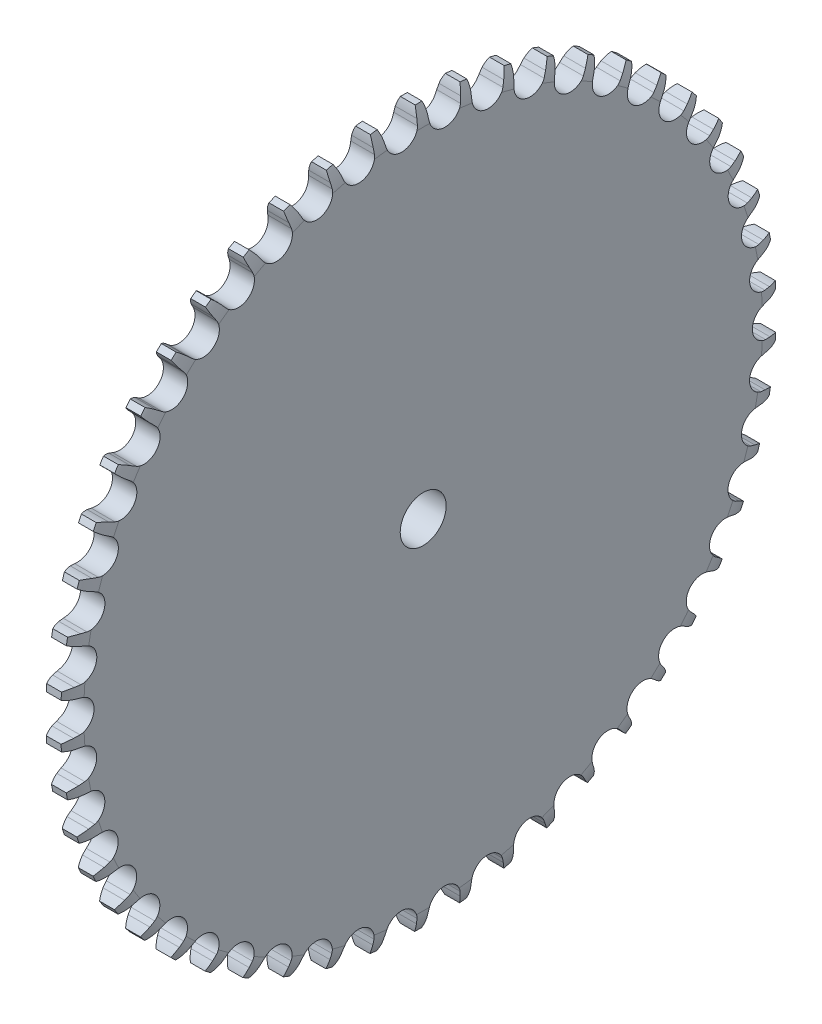
SolidWorks part; units mm, degrees
ref_plane "Front Plane" through (0, 0, 0) normal (0, 0, 1) x (1, 0, 0)
ref_plane "Top Plane" through (0, 0, 0) normal (0, 1, 0) x (1, 0, 0)
ref_plane "Right Plane" through (0, 0, 0) normal (1, 0, 0) x (0, 0, -1)
sketch "Sketch1" plane through (0, 0, 0) normal (0, 0, 1) x (1, 0, 0)
  line L0 (0, 0) -> (0, 73.8414)
  line L1 (-1.0423, 77.85) -> (-4.2577, 77.85)
  line L2 (-5.3, 73.8414) -> (-5.3, 20)
  line L3 (-5.3, 20) -> (-35.3, 20)
  line L4 (-35.3, 20) -> (-35.3, 0)
  line L5 (-35.3, 0) -> (0, 0)
  line L6 (0, 0) -> (22.8181, 0) construction
  arc A0 (-5.3, 73.8414) -> (-4.2577, 77.85) centre (4.6895, 73.3839) cw
  arc A1 (0, 73.8414) -> (-1.0423, 77.85) centre (-9.9895, 73.3839) ccw
  dimension "D5" = 10
  dimension "D1" = 35.3
  dimension "D2" = 30
  dimension "D3" = 20
  dimension "D4" = 155.7
revolve "Revolve1" add sketch "Sketch1" angle 360 about L6
sketch "Sketch2" plane through (-35.3, 0, 0) normal (-1, 0, 0) x (0, 0, 1)
  circle A0 centre (0, 0) radius 5
  dimension "D1" = 10
extrude "Cut-Extrude1" cut sketch "Sketch2" against normal blind 93
sketch "Sketch4" plane through (-35.3, 0, 0) normal (-1, 0, 0) x (0, 0, 1)
  line L0 (0, 0) -> (0, 75.845) construction
  line L1 (0, 0) -> (-4.7625, 74.9583) construction
  line L2 (0, 0) -> (4.7625, 74.9583) construction
  line L3 (-1.1687, 75.836) -> (-1.2768, 74.6426)
  line L4 (1.1687, 75.836) -> (1.2884, 75.3836)
  line L5 (-8.4385, 75.3741) -> (-8.1803, 74.204)
  arc A0 (-8.4385, 75.3741) -> (-1.1687, 75.836) centre (0, 0) ccw
  arc A1 (-8.1803, 74.204) -> (-1.2768, 74.6426) centre (-4.7625, 74.9583) ccw
  circle A2 centre (4.7625, 74.9583) radius 3.5
  arc A3 (-1.1687, 75.836) -> (-0.796, 77.8459) centre (9.7865, 74.844) cw
  circle A4 centre (0, 0) radius 77.85 construction
  arc A5 (1.1687, 75.836) -> (0.796, 77.8459) centre (-9.7865, 74.844) ccw
  arc A6 (-8.4385, 75.3741) -> (-9.0626, 77.3207) centre (-19.18, 73.0036) ccw
  arc A7 (-9.0626, 77.3207) -> (-0.796, 77.8459) centre (0, 0) cw
  dimension "D1" = 151.69
  dimension "D3" = 7
  dimension "D4" = 7
  dimension "D6" = 11
  dimension "D2" = 9.525
  dimension "D5" = 20
extrude "Cut-Extrude2" cut sketch "Sketch4" against normal blind 50 contours A7 A3 L3 A1 L5 A6
pattern_circular "CirPattern2" count 50 over 360 about axis through (0, 0, 0) along (1, 0, 0) of "Cut-Extrude2"
sketch "Sketch5" plane through (-35.3, 0, 0) normal (-1, 0, 0) x (0, 0, 1)
  line L1 (0, 7) -> (-2.85, 7)
  line L2 (-2.85, 7) -> (-2.85, 9.5)
  line L3 (-2.85, 9.5) -> (2.85, 9.5)
  line L4 (2.85, 9.5) -> (2.85, 7)
  line L5 (2.85, 7) -> (0, 7)
  line L7 (6.0622, -3.5) -> (7.4872, -1.0318)
  line L8 (7.4872, -1.0318) -> (9.6522, -2.2818)
  line L9 (9.6522, -2.2818) -> (6.8022, -7.2182)
  line L10 (6.8022, -7.2182) -> (4.6372, -5.9682)
  line L11 (4.6372, -5.9682) -> (6.0622, -3.5)
  line L13 (-6.0622, -3.5) -> (-7.4872, -1.0318)
  line L14 (-7.4872, -1.0318) -> (-9.6522, -2.2818)
  line L15 (-9.6522, -2.2818) -> (-6.8022, -7.2182)
  line L16 (-6.8022, -7.2182) -> (-4.6372, -5.9682)
  line L17 (-4.6372, -5.9682) -> (-6.0622, -3.5)
  dimension "D6" = 5.7
  dimension "D7" = 2.5
  dimension "D8" = 2.85
  dimension "D9" = 2.85
  dimension "D10" = 2.5
  dimension "D11" = 5.7
  dimension "D12" = 2.5
  dimension "D13" = 5.7
  dimension "D14" = 2.85
extrude "Cut-Extrude3" cut sketch "Sketch5" against normal blind 12.85
ref_plane "Plane1" through (0, 20, 0) normal (0, 1, 0) x (1, 0, 0)
sketch "Sketch6" plane through (0, 20, 0) normal (0, 1, 0) x (1, 0, 0)
  circle A0 centre (-20.3, 0) radius 3
  dimension "D1" = 6
extrude "Cut-Extrude4" cut sketch "Sketch6" against normal blind 4.5
sketch "Sketch7" plane through (0, 20, 0) normal (0, 1, 0) x (1, 0, 0)
  circle A0 centre (-20.3, 0) radius 1.95
  dimension "D1" = 3.9
extrude "Cut-Extrude5" cut sketch "Sketch7" against normal up to next
sketch "Sketch8" plane through (-35.3, 0, 0) normal (-1, 0, 0) x (0, 0, 1)
  line L0 (-2.85, 9.5) -> (2.85, 9.5)
  line L1 (2.85, 9.5) -> (2.85, 7)
  line L2 (2.85, 7) -> (-2.85, 7)
  line L3 (-2.85, 7) -> (-2.85, 9.5)
  line L4 (7.4872, -1.0318) -> (4.6372, -5.9682)
  line L5 (4.6372, -5.9682) -> (6.8022, -7.2182)
  line L6 (4.6372, -5.9682) -> (6.8022, -7.2182) construction
  line L7 (4.6372, -5.9682) -> (6.8022, -7.2182) construction
  line L8 (6.8022, -7.2182) -> (9.6522, -2.2818)
  line L9 (9.6522, -2.2818) -> (7.4872, -1.0318)
  line L10 (-7.4872, -1.0318) -> (-9.6522, -2.2818)
  line L11 (-9.6522, -2.2818) -> (-6.8022, -7.2182)
  line L12 (-6.8022, -7.2182) -> (-4.6372, -5.9682)
  line L13 (-4.6372, -5.9682) -> (-7.4872, -1.0318)
extrude "Cut-Extrude6" cut sketch "Sketch8" against normal blind 17.85
ref_plane "Plane2" through (0, -10, 17.3205) normal (0, -0.5, 0.866) x (-1, 0, 0)
sketch "Sketch9" plane through (0, -10, 17.3205) normal (0, -0.5, 0.866) x (-1, 0, 0)
  circle A0 centre (20.3, 0) radius 3
  dimension "D1" = 6
extrude "Cut-Extrude7" cut sketch "Sketch9" against normal blind 4.5
sketch "Sketch10" plane through (0, -10, 17.3205) normal (0, -0.5, 0.866) x (-1, 0, 0)
  circle A0 centre (20.3, 0) radius 1.95
  dimension "D1" = 3.9
extrude "Cut-Extrude8" cut sketch "Sketch10" against normal up to next
sketch "Sketch11" plane through (0, -10, 17.3205) normal (0, -0.5, 0.866) x (-1, 0, 0)
  circle A0 centre (20.3, 0) radius 1.95
  dimension "D1" = 3.9
extrude "Cut-Extrude9" cut sketch "Sketch11" against normal up to next
ref_plane "Plane3" through (0, -10, -17.3205) normal (0, -0.5, -0.866) x (-1, 0, 0)
sketch "Sketch12" plane through (0, -10, -17.3205) normal (0, -0.5, -0.866) x (-1, 0, 0)
  circle A0 centre (20.3, 0) radius 3
  dimension "D1" = 6
extrude "Cut-Extrude10" cut sketch "Sketch12" against normal blind 4.5
sketch "Sketch13" plane through (0, -10, -17.3205) normal (0, -0.5, -0.866) x (-1, 0, 0)
  circle A0 centre (20.3, 0) radius 1.95
  dimension "D1" = 3.9
extrude "Cut-Extrude11" cut sketch "Sketch13" against normal up to next
sketch "Sketch14" plane through (0, -10, -17.3205) normal (0, -0.5, -0.866) x (-1, 0, 0)
  circle A0 centre (20.3, 0) radius 1.95
  dimension "D1" = 3.9
extrude "Cut-Extrude12" cut sketch "Sketch14" against normal up to next
